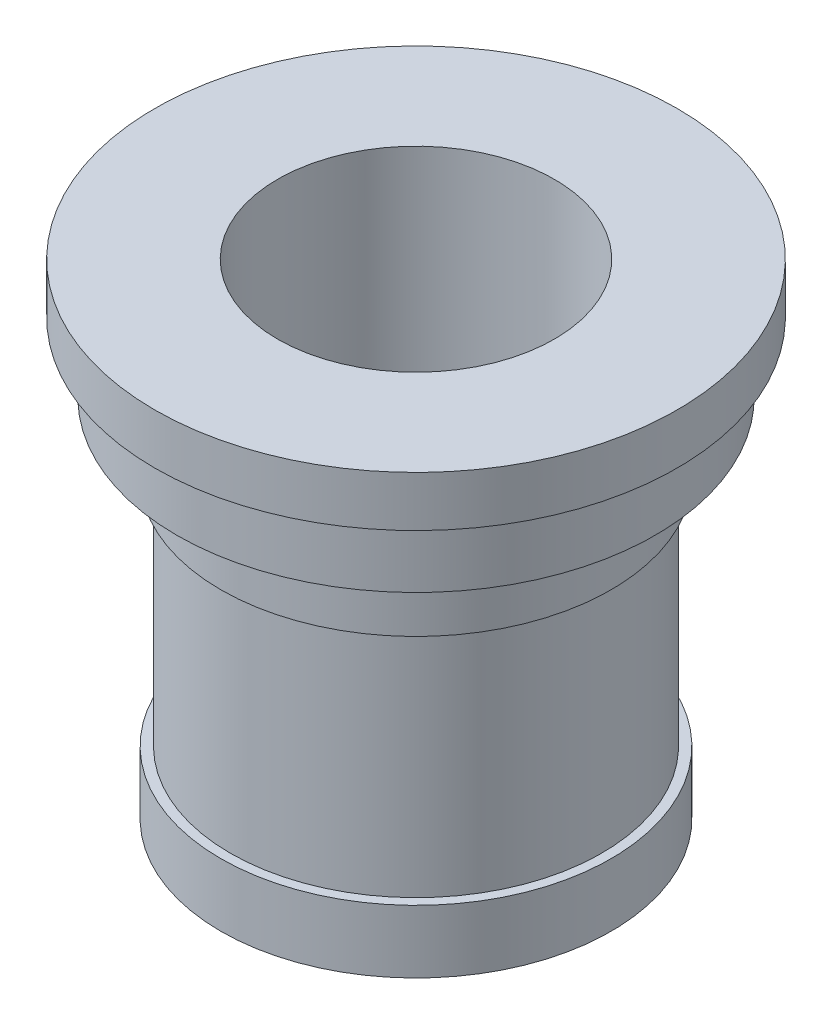
SolidWorks part; units mm, degrees
ref_plane "Front Plane" through (0, 0, 0) normal (0, 0, 1) x (1, 0, 0)
ref_plane "Top Plane" through (0, 0, 0) normal (0, 1, 0) x (1, 0, 0)
ref_plane "Right Plane" through (0, 0, 0) normal (1, 0, 0) x (0, 0, -1)
sketch "Sketch1" plane through (0, 0, 0) normal (0, 0, 1) x (1, 0, 0)
  line L0 (0, 42.0139) -> (0, -42.0139) construction
  line L1 (22, 0) -> (22, 77)
  line L2 (22, 77) -> (41.5, 77)
  line L3 (41.5, 77) -> (41.5, 69)
  line L4 (41.5, 69) -> (38, 69)
  line L5 (38, 69) -> (38, 58)
  line L6 (38, 58) -> (31, 58)
  line L7 (31, 58) -> (31, 47)
  line L8 (31, 47) -> (29.5, 47)
  line L9 (29.5, 47) -> (29.5, 10)
  line L10 (29.5, 10) -> (31, 10)
  line L11 (31, 10) -> (31, 0)
  line L12 (31, 0) -> (22, 0)
  dimension "D1" = 44
  dimension "D2" = 62
  dimension "D3" = 59
  dimension "D4" = 62
  dimension "D5" = 76
  dimension "D6" = 83
  dimension "D7" = 77
  dimension "D8" = 8
  dimension "D9" = 11
  dimension "D10" = 11
  dimension "D11" = 37
  dimension "D12" = 10
revolve "Revolve1" add sketch "Sketch1" angle 360 about L0
sketch "Sketch3" plane through (0, 0, 0) normal (0, -1, 0) x (1, 0, 0)
  circle A0 centre (-22, 0) radius 1.5
  circle A1 centre (0, 0) radius 22 construction
  dimension "D1" = 3
extrude "Cut-Extrude1" cut sketch "Sketch3" against normal blind 5
